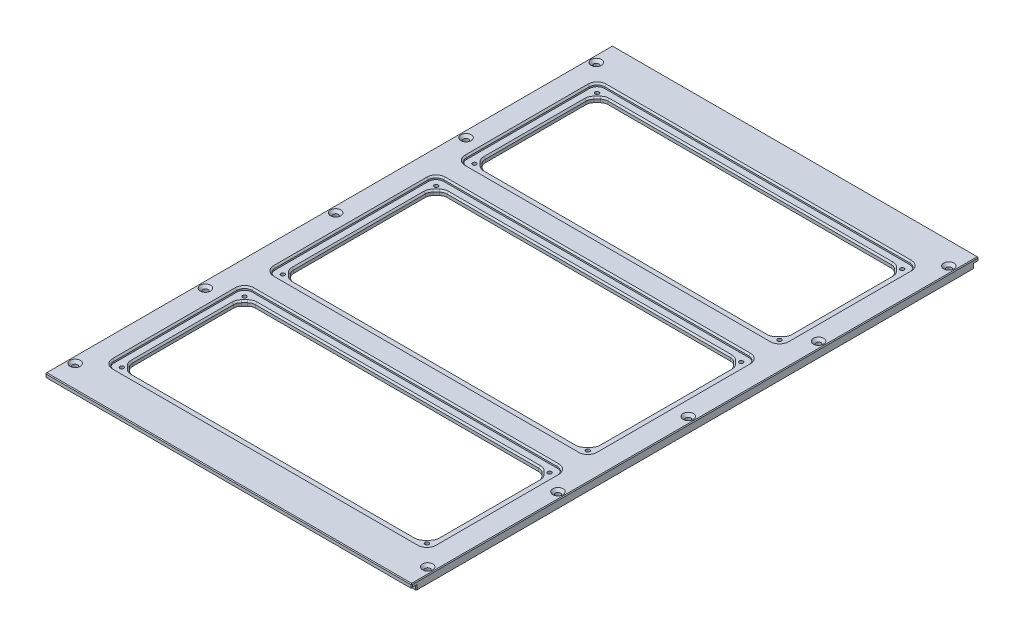
SolidWorks part; units mm, degrees
material "2014 Alloy"
ref_plane "Front Plane" through (0, 0, 0) normal (0, 0, 1) x (1, 0, 0)
ref_plane "Top Plane" through (0, 0, 0) normal (0, 1, 0) x (1, 0, 0)
ref_plane "Right Plane" through (0, 0, 0) normal (1, 0, 0) x (0, 0, -1)
sketch "Sketch1" plane through (0, 0, 0) normal (0, 1, 0) x (1, 0, 0)
  line L1 (0, 0) -> (-239, 0)
  line L2 (0, 0) -> (0, 370)
  line L3 (0, 370) -> (-239, 370)
  line L4 (-239, 0) -> (-239, 370)
  dimension "D1" = 239
  dimension "D2" = 370
extrude "Boss-Extrude1" add sketch "Sketch1" along normal blind 5
hole_wizard "CSK for M3 Hex Socket Countersunk Cap Screw1" positions "Sketch3" profile "Sketch2" countersink size "M3" standard "ISO" end condition through all
sketch "Sketch3" plane through (0, 5, 0) normal (0, 1, 0) x (1, 0, 0)
  line L0 (-239, 185) -> (0, 185) construction
  line L1 (-239, 370) -> (-239, 0) construction
  line L2 (0, 0) -> (0, 370) construction
  point P0 (-4.5, 15)
  point P2 (-4.5, 100)
  point P4 (-4.5, 185)
  point P6 (-4.5, 270)
  point P8 (-4.5, 355)
  dimension "D1" = 85
  dimension "D2" = 85
  dimension "D3" = 85
  dimension "D4" = 85
  dimension "D5" = 4.5
sketch "Sketch2" plane through (-4.5, 5, -15) normal (1, 0, 0) x (0, 0, 1)
  line L0 (0, 0) -> (0, 5)
  line L1 (0, 5) -> (1.7, 5)
  line L2 (1.7, 5) -> (1.7, 1.66)
  line L3 (1.7, 1.66) -> (3.36, 0)
  line L5 (3.36, 0) -> (0, 0)
  line L6 (-1.7, 1.66) -> (-3.36, 0) construction
  line L11 (0, -6.35) -> (0, 107.95) construction
  dimension "Thru Hole Dia." = 3.4
  dimension "Thru Hole Depth" = 5
  dimension "Near C'Sink Dia." = 6.72
  dimension "Near C'Sink Angle" = 90
sketch "Sketch4" plane through (0, 5, 0) normal (0, 1, 0) x (1, 0, 0)
  line L0 (-119.5, 0) -> (-119.5, 370) construction
  line L1 (-239, 0) -> (0, 0) construction
  line L2 (0, 370) -> (-239, 370) construction
  line L3 (-239, 185) -> (0, 185) construction
  line L4 (-239, 370) -> (-239, 0) construction
  line L5 (0, 0) -> (0, 370) construction
  line L6 (-224, 255) -> (-224, 345)
  line L7 (-224, 240) -> (-15, 240)
  line L8 (-224, 240) -> (-224, 130)
  line L9 (-224, 130) -> (-15, 130)
  line L10 (-15, 240) -> (-15, 130)
  line L11 (-224, 240) -> (-15, 130) construction
  line L12 (-224, 130) -> (-15, 240) construction
  line L13 (-15, 115) -> (-224, 115)
  line L14 (-15, 115) -> (-15, 25)
  line L15 (-15, 25) -> (-224, 25)
  line L16 (-224, 115) -> (-224, 25)
  line L17 (-15, 115) -> (-224, 25) construction
  line L18 (-15, 25) -> (-224, 115) construction
  line L19 (-15, 255) -> (-224, 255)
  line L20 (-15, 255) -> (-15, 345)
  line L21 (-15, 345) -> (-224, 345)
  point P12 (-119.5, 185)
  point P17 (-119.5, 70)
  dimension "D1" = 15
  dimension "D2" = 130
  dimension "D3" = 15
  dimension "D4" = 15
  dimension "D5" = 25
extrude "Cut-Extrude1" cut sketch "Sketch4" against normal blind 2
sketch "Sketch5" plane through (0, 3, 0) normal (0, 1, 0) x (1, 0, 0)
  line L0 (-224, 185) -> (-15, 185) construction
  line L1 (-224, 240) -> (-224, 130) construction
  line L2 (-15, 130) -> (-15, 240) construction
  line L3 (-119.5, 25) -> (-119.5, 185) construction
  line L4 (-224, 25) -> (-15, 25) construction
  line L5 (-15, 240) -> (-224, 240) construction
  line L6 (-219, 235) -> (-20, 235)
  line L7 (-219, 235) -> (-219, 135)
  line L8 (-219, 135) -> (-20, 135)
  line L9 (-20, 235) -> (-20, 135)
  line L10 (-219, 235) -> (-20, 135) construction
  line L11 (-219, 135) -> (-20, 235) construction
  line L12 (-224, 70) -> (-15, 70) construction
  line L13 (-224, 115) -> (-224, 25) construction
  line L14 (-15, 25) -> (-15, 115) construction
  line L15 (-15, 115) -> (-224, 115) construction
  line L16 (-219, 110) -> (-20, 110)
  line L17 (-219, 110) -> (-219, 30)
  line L18 (-219, 30) -> (-20, 30)
  line L19 (-20, 110) -> (-20, 30)
  line L20 (-219, 110) -> (-20, 30) construction
  line L21 (-219, 30) -> (-20, 110) construction
  line L22 (-20, 260) -> (-20, 340)
  line L23 (-219, 340) -> (-20, 340)
  line L24 (-219, 260) -> (-219, 340)
  line L25 (-219, 260) -> (-20, 260)
  point P22 (-119.5, 70)
  dimension "D1" = 5
  dimension "D2" = 5
  dimension "D3" = 5
  dimension "D4" = 5
extrude "Cut-Extrude2" cut sketch "Sketch5" against normal through all
chamfer "Chamfer1" distance 5 angle 45 12 edges at (-20, 1.5, -30) (-20, 1.5, -110) (-219, 1.5, -110) (-219, 1.5, -30) (-219, 1.5, -135) (-20, 1.5, -135) (-20, 1.5, -235) (-219, 1.5, -235) (-219, 1.5, -260) (-20, 1.5, -260) (-20, 1.5, -340) (-219, 1.5, -340)
fillet "Fillet1" radius 5 36 edges at (-15, 4, -115) (-224, 4, -115) (-224, 4, -25) (-15, 4, -25) (-15, 4, -130) (-224, 4, -130) (-224, 4, -240) (-15, 4, -240) (-15, 4, -255) (-224, 4, -255) (-224, 4, -345) (-15, 4, -345) (-214, 1.5, -340) (-219, 1.5, -335) (-214, 1.5, -260) (-219, 1.5, -265) (-214, 1.5, -135) (-219, 1.5, -140) (-25, 1.5, -260) (-20, 1.5, -265) (-25, 1.5, -235) (-20, 1.5, -230) (-20, 1.5, -105) (-25, 1.5, -110) (-214, 1.5, -110) (-219, 1.5, -105) (-219, 1.5, -35) (-214, 1.5, -30) (-20, 1.5, -35) (-25, 1.5, -30) (-25, 1.5, -340) (-20, 1.5, -335) (-219, 1.5, -230) (-214, 1.5, -235) (-25, 1.5, -135) (-20, 1.5, -140)
sketch "Sketch6" plane through (0, 0, 0) normal (0, -1, 0) x (1, 0, 0)
  line L0 (-239, -185) -> (0, -185) construction
  line L1 (-239, -370) -> (-239, 0) construction
  line L2 (0, 0) -> (0, -370) construction
  line L3 (-224, -122.5) -> (-169, -122.5) construction
  line L4 (-224, -115.5) -> (-169, -115.5)
  line L5 (-224, -129.5) -> (-169, -129.5)
  line L6 (-147, -122.5) -> (-92, -122.5) construction
  line L7 (-147, -115.5) -> (-92, -115.5)
  line L8 (-147, -129.5) -> (-92, -129.5)
  line L9 (-70, -122.5) -> (-15, -122.5) construction
  line L10 (-70, -115.5) -> (-15, -115.5)
  line L11 (-70, -129.5) -> (-15, -129.5)
  line L12 (-70, -247.5) -> (-15, -247.5) construction
  line L13 (-70, -254.5) -> (-15, -254.5)
  line L14 (-70, -240.5) -> (-15, -240.5)
  line L15 (-147, -247.5) -> (-92, -247.5) construction
  line L16 (-147, -254.5) -> (-92, -254.5)
  line L17 (-147, -240.5) -> (-92, -240.5)
  line L18 (-224, -247.5) -> (-169, -247.5) construction
  line L19 (-224, -254.5) -> (-169, -254.5)
  line L20 (-224, -240.5) -> (-169, -240.5)
  line L22 (-27.0711, -110) -> (-211.9289, -110) construction
  line L23 (-196.799, -9.8033) -> (-160.0685, -23.8033)
  line L24 (-159, -4) -> (-195.7305, -4)
  line L25 (-156, -21) -> (-156, -7)
  line L26 (-183.201, -18.1967) -> (-219.9315, -4.1967)
  line L27 (-221, -24) -> (-184.2695, -24)
  line L28 (-224, -7) -> (-224, -21)
  line L29 (-151, -7) -> (-151, -21)
  line L30 (-114.3973, -4) -> (-148, -4)
  line L31 (-146.8462, -23.7693) -> (-113.2436, -9.7693)
  line L32 (-90.9958, -24) -> (-124.5984, -24)
  line L33 (-92.1495, -4.2307) -> (-125.7522, -18.2307)
  line L34 (-87.9958, -21) -> (-87.9958, -7)
  line L35 (-79.9958, -4) -> (-42.0888, -4)
  line L36 (-82.9958, -21) -> (-82.9958, -7)
  line L37 (-41.0495, -9.8142) -> (-78.9564, -23.8142)
  line L38 (-55.0575, -18.1858) -> (-17.1506, -4.1858)
  line L39 (-18.4099, -24) -> (-54.0182, -24)
  line L40 (-13.1508, -7.4861) -> (-15.4495, -21.4861)
  line L52 (-13.1508, -362.5139) -> (-15.4495, -348.5139)
  line L53 (-18.4099, -346) -> (-54.0182, -346)
  line L54 (-55.0575, -351.8142) -> (-17.1506, -365.8142)
  line L55 (-41.0495, -360.1858) -> (-78.9564, -346.1858)
  line L56 (-82.9958, -349) -> (-82.9958, -363)
  line L57 (-79.9958, -366) -> (-42.0888, -366)
  line L58 (-87.9958, -349) -> (-87.9958, -363)
  line L59 (-92.1495, -365.7693) -> (-125.7522, -351.7693)
  line L60 (-90.9958, -346) -> (-124.5984, -346)
  line L61 (-146.8462, -346.2307) -> (-113.2436, -360.2307)
  line L62 (-114.3973, -366) -> (-148, -366)
  line L63 (-151, -363) -> (-151, -349)
  line L64 (-224, -363) -> (-224, -349)
  line L65 (-221, -346) -> (-184.2695, -346)
  line L66 (-117.9958, -373) -> (-117.9958, -338) construction
  line L67 (-183.201, -351.8033) -> (-219.9315, -365.8033)
  line L68 (-156, -349) -> (-156, -363)
  line L69 (-159, -366) -> (-195.7305, -366)
  line L70 (-196.799, -360.1967) -> (-160.0685, -346.1967)
  line L71 (0, -370) -> (-239, -370) construction
  line L89 (-27.0711, -340) -> (-211.9289, -340) construction
  arc A0 (-224, -115.5) -> (-224, -129.5) centre (-224, -122.5) ccw
  arc A1 (-169, -129.5) -> (-169, -115.5) centre (-169, -122.5) ccw
  arc A2 (-147, -115.5) -> (-147, -129.5) centre (-147, -122.5) ccw
  arc A3 (-92, -129.5) -> (-92, -115.5) centre (-92, -122.5) ccw
  arc A4 (-70, -115.5) -> (-70, -129.5) centre (-70, -122.5) ccw
  arc A5 (-15, -129.5) -> (-15, -115.5) centre (-15, -122.5) ccw
  arc A6 (-70, -254.5) -> (-70, -240.5) centre (-70, -247.5) cw
  arc A7 (-15, -240.5) -> (-15, -254.5) centre (-15, -247.5) cw
  arc A8 (-147, -254.5) -> (-147, -240.5) centre (-147, -247.5) cw
  arc A9 (-92, -240.5) -> (-92, -254.5) centre (-92, -247.5) cw
  arc A10 (-224, -254.5) -> (-224, -240.5) centre (-224, -247.5) cw
  arc A11 (-169, -240.5) -> (-169, -254.5) centre (-169, -247.5) cw
  arc A12 (-13.1508, -7.4861) -> (-17.1506, -4.1858) centre (-16.1112, -7) ccw
  arc A13 (-15.4495, -21.4861) -> (-18.4099, -24) centre (-18.4099, -21) cw
  arc A14 (-54.0182, -24) -> (-55.0575, -18.1858) centre (-54.0182, -21) cw
  arc A15 (-41.0495, -9.8142) -> (-42.0888, -4) centre (-42.0888, -7) ccw
  arc A16 (-78.9564, -23.8142) -> (-82.9958, -21) centre (-79.9958, -21) cw
  arc A17 (-82.9958, -7) -> (-79.9958, -4) centre (-79.9958, -7) cw
  arc A18 (-87.9958, -7) -> (-92.1495, -4.2307) centre (-90.9958, -7) ccw
  arc A19 (-87.9958, -21) -> (-90.9958, -24) centre (-90.9958, -21) cw
  arc A20 (-125.7522, -18.2307) -> (-124.5984, -24) centre (-124.5984, -21) ccw
  arc A21 (-113.2436, -9.7693) -> (-114.3973, -4) centre (-114.3973, -7) ccw
  arc A22 (-146.8462, -23.7693) -> (-151, -21) centre (-148, -21) cw
  arc A23 (-148, -4) -> (-151, -7) centre (-148, -7) ccw
  arc A24 (-156, -7) -> (-159, -4) centre (-159, -7) ccw
  arc A25 (-156, -21) -> (-160.0685, -23.8033) centre (-159, -21) cw
  arc A26 (-195.7305, -4) -> (-196.799, -9.8033) centre (-195.7305, -7) ccw
  arc A27 (-184.2695, -24) -> (-183.201, -18.1967) centre (-184.2695, -21) ccw
  arc A28 (-224, -7) -> (-219.9315, -4.1967) centre (-221, -7) cw
  arc A29 (-224, -21) -> (-221, -24) centre (-221, -21) ccw
  arc A36 (-224, -349) -> (-221, -346) centre (-221, -349) cw
  arc A37 (-224, -363) -> (-219.9315, -365.8033) centre (-221, -363) ccw
  arc A38 (-184.2695, -346) -> (-183.201, -351.8033) centre (-184.2695, -349) cw
  arc A39 (-195.7305, -366) -> (-196.799, -360.1967) centre (-195.7305, -363) cw
  arc A40 (-156, -349) -> (-160.0685, -346.1967) centre (-159, -349) ccw
  arc A41 (-156, -363) -> (-159, -366) centre (-159, -363) cw
  arc A42 (-148, -366) -> (-151, -363) centre (-148, -363) cw
  arc A43 (-146.8462, -346.2307) -> (-151, -349) centre (-148, -349) ccw
  arc A44 (-113.2436, -360.2307) -> (-114.3973, -366) centre (-114.3973, -363) cw
  arc A45 (-125.7522, -351.7693) -> (-124.5984, -346) centre (-124.5984, -349) cw
  arc A46 (-87.9958, -349) -> (-90.9958, -346) centre (-90.9958, -349) ccw
  arc A47 (-87.9958, -363) -> (-92.1495, -365.7693) centre (-90.9958, -363) cw
  arc A48 (-82.9958, -363) -> (-79.9958, -366) centre (-79.9958, -363) ccw
  arc A49 (-78.9564, -346.1858) -> (-82.9958, -349) centre (-79.9958, -349) ccw
  arc A50 (-41.0495, -360.1858) -> (-42.0888, -366) centre (-42.0888, -363) cw
  arc A51 (-54.0182, -346) -> (-55.0575, -351.8142) centre (-54.0182, -349) ccw
  arc A52 (-15.4495, -348.5139) -> (-18.4099, -346) centre (-18.4099, -349) ccw
  arc A53 (-13.1508, -362.5139) -> (-17.1506, -365.8142) centre (-16.1112, -363) cw
  point P12 (-196.5, -122.5)
  point P17 (-119.5, -122.5)
  point P24 (-42.5, -122.5)
  point P31 (-42.5, -247.5)
  point P38 (-119.5, -247.5)
  point P45 (-196.5, -247.5)
  dimension "D20" = 3
  dimension "D6" = 7
  dimension "D7" = 7
  dimension "D8" = 7
  dimension "D9" = 55
  dimension "D10" = 55
  dimension "D11" = 55
  dimension "D12" = 22
  dimension "D13" = 12.5
  dimension "D16" = 30
  dimension "D17" = 3
  dimension "D18" = 5
  dimension "D19" = 3
  dimension "D21" = 4
  dimension "D22" = 6
  dimension "D24" = 63.0042
  dimension "D25" = 68
  dimension "D33" = 5
  dimension "D34" = 3
extrude "Cut-Extrude3" cut sketch "Sketch6" against normal blind 4
sketch "Sketch7" plane through (0, 5, 0) normal (0, 1, 0) x (1, 0, 0)
  line L0 (-119.5, 0) -> (-119.5, 370) construction
  line L1 (-239, 0) -> (0, 0) construction
  line L2 (0, 370) -> (-239, 370) construction
sketch "Sketch8" plane through (0, 0, 0) normal (0, 0, 1) x (1, 0, 0)
  line L0 (-119.5, 5) -> (-119.5, 0) construction
  line L1 (-239, 0) -> (0, 0) construction
ref_plane "Plane1" through (-119.5, 0, 0) normal (-1, 0, 0) x (0, 0, 1)
mirror "Mirror1" about plane through (-119.5, 0, 0) normal (-1, 0, 0) of "CSK for M3 Hex Socket Countersunk Cap Screw1"
hole_wizard "M3 Tapped Hole1" positions "Sketch10" profile "Sketch9" tap size "M3" standard "ISO"
sketch "Sketch10" plane through (0, 3, 0) normal (0, 1, 0) x (1, 0, 0)
  arc A2 (-224, 30) -> (-219, 25) centre (-219, 30) ccw construction
  arc A3 (-219, 115) -> (-224, 110) centre (-219, 110) ccw construction
  arc A6 (-224, 135) -> (-219, 130) centre (-219, 135) ccw construction
  arc A7 (-219, 240) -> (-224, 235) centre (-219, 235) ccw construction
  arc A8 (-224, 260) -> (-219, 255) centre (-219, 260) ccw construction
  arc A9 (-219, 345) -> (-224, 340) centre (-219, 340) ccw construction
  point P0 (-219, 110)
  point P2 (-219, 30)
  point P4 (-219, 135)
  point P6 (-219, 235)
  point P8 (-219, 260)
  point P10 (-219, 340)
sketch "Sketch9" plane through (-219, 3, -110) normal (1, 0, 0) x (0, 0, 1)
  line L0 (0, 0) -> (0, 15.7511)
  line L1 (0, 15.7511) -> (1.25, 15)
  line L2 (1.25, 15) -> (1.25, 0)
  line L5 (1.25, 0) -> (0, 0)
  line L10 (0, 15.7511) -> (-1.25, 15) construction
  line L11 (0, -6.35) -> (0, 107.95) construction
  dimension "Tap Drill Dia." = 2.5
  dimension "Tap Drill Depth" = 15
  dimension "Drill Angle" = 118
cosmetic thread "Hole Thread1" parameters "D1"=3, "D2"=3
cosmetic thread "Hole Thread2" parameters "D1"=3, "D2"=3
cosmetic thread "Hole Thread3" parameters "D1"=3, "D2"=3
cosmetic thread "Hole Thread4" parameters "D1"=3, "D2"=3
cosmetic thread "Hole Thread5" parameters "D1"=3, "D2"=3
cosmetic thread "Hole Thread6" parameters "D1"=3, "D2"=3
mirror "Mirror2" about plane through (-119.5, 0, 0) normal (-1, 0, 0) of "M3 Tapped Hole1"
chamfer "Chamfer2" distance 1 angle 45 72 edges at (-119.5, 3, -30) (-25.1577, 3, -30.3806) (-213.8423, 3, -30.3806) (-22.5, 3, -32.5) (-216.5, 3, -32.5) (-20.3806, 3, -35.1577) (-218.6194, 3, -35.1577) (-20, 3, -70) (-219, 3, -70) (-20.3806, 3, -104.8423) (-218.6194, 3, -104.8423) (-22.5, 3, -107.5) (-216.5, 3, -107.5) (-25.1577, 3, -109.6194) (-213.8423, 3, -109.6194) (-119.5, 3, -110) (-119.5, 3, -135) (-25.1577, 3, -135.3806) (-213.8423, 3, -135.3806) (-22.5, 3, -137.5) (-216.5, 3, -137.5) (-20.3806, 3, -140.1577) (-218.6194, 3, -140.1577) (-20, 3, -185) (-219, 3, -185) (-20.3806, 3, -229.8423) (-218.6194, 3, -229.8423) (-22.5, 3, -232.5) (-216.5, 3, -232.5) (-25.1577, 3, -234.6194) (-213.8423, 3, -234.6194) (-119.5, 3, -235) (-119.5, 3, -340) (-213.8423, 3, -339.6194) (-25.1577, 3, -339.6194) (-216.5, 3, -337.5) (-22.5, 3, -337.5) (-218.6194, 3, -334.8423) (-20.3806, 3, -334.8423) (-219, 3, -300) (-20, 3, -300) (-218.6194, 3, -265.1577) (-20.3806, 3, -265.1577) (-216.5, 3, -262.5) (-22.5, 3, -262.5) (-213.8423, 3, -260.3806) (-25.1577, 3, -260.3806) (-119.5, 3, -260) (-119.5, 5, -345) (-222.5355, 5, -343.5355) (-16.4645, 5, -343.5355) (-224, 5, -300) (-15, 5, -300) (-222.5355, 5, -256.4645) (-16.4645, 5, -256.4645) (-119.5, 5, -255) (-119.5, 5, -25) (-16.4645, 5, -26.4645) (-222.5355, 5, -26.4645) (-15, 5, -70) (-224, 5, -70) (-16.4645, 5, -113.5355) (-222.5355, 5, -113.5355) (-119.5, 5, -115) (-119.5, 5, -240) (-222.5355, 5, -238.5355) (-16.4645, 5, -238.5355) (-224, 5, -185) (-15, 5, -185) (-222.5355, 5, -131.4645) (-16.4645, 5, -131.4645) (-119.5, 5, -130)
sketch "Sketch12" plane through (0, 0, 0) normal (0, -1, 0) x (1, 0, 0)
  line L0 (-239, -370) -> (-239, 0) construction
  line L1 (0, 0) -> (-239, 0)
  line L2 (0, 0) -> (0, -3)
  line L3 (0, -3) -> (-239, -3)
  line L4 (-239, 0) -> (-239, -3)
  line L5 (0, 0) -> (0, -370) construction
  line L6 (-239, -370) -> (0, -370)
  line L7 (-239, -370) -> (-239, -367)
  line L8 (-239, -367) -> (0, -367)
  line L9 (0, -370) -> (0, -367)
  dimension "D1" = 3
  dimension "D2" = 3
extrude "Cut-Extrude7" cut sketch "Sketch12" against normal blind 2.5
chamfer "Chamfer3" distance 0.5 angle 45 16 edges at (-119.5, 5, 0) (-239, 5, -185) (-119.5, 5, -370) (0, 5, -185) (-239, 1.25, -3) (-239, 2.5, -1.5) (0, 1.25, -3) (0, 2.5, -1.5) (0, 1.25, -367) (0, 2.5, -368.5) (-239, 1.25, -367) (-239, 2.5, -368.5) (-239, 3.75, -370) (-239, 3.75, 0) (0, 3.75, -370) (0, 3.75, 0)
equation "\"0.5mmmm\"=1"
